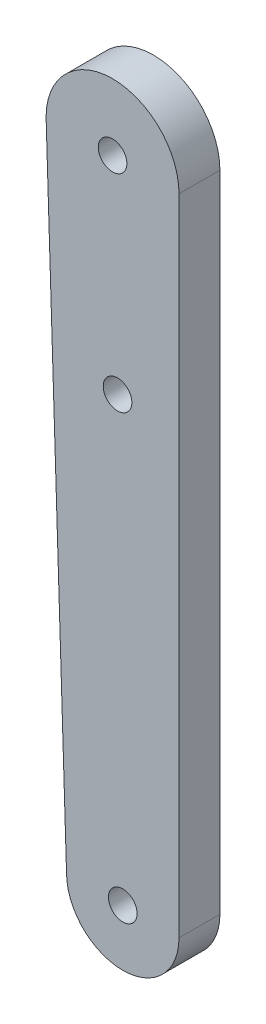
SolidWorks part; units mm, degrees
ref_plane "Front Plane" through (0, 0, 0) normal (0, 0, 1) x (1, 0, 0)
ref_plane "Top Plane" through (0, 0, 0) normal (0, 1, 0) x (1, 0, 0)
ref_plane "Right Plane" through (0, 0, 0) normal (1, 0, 0) x (0, 0, -1)
sketch "Sketch1" plane through (0, 0, 0) normal (0, 0, 1) x (1, 0, 0)
  line L6 (-0.0007, 1.9933) -> (-0.0007, 65.0161)
  line L7 (-13.0007, 65.0161) -> (-11.0007, 1.9933)
  arc A0 (-0.0007, 65.0161) -> (-13.0007, 65.0161) centre (-6.5007, 65.0161) ccw
  arc A1 (-11.0007, 1.9933) -> (-0.0007, 1.9933) centre (-5.5007, 1.9933) ccw
  circle A2 centre (-6.5007, 65.0161) radius 1.4
  circle A3 centre (-5.5007, 1.9933) radius 1.4
  circle A4 centre (-6.0128, 45.0161) radius 1.4
  point P8 (-5.0007, -3.4839)
  point P11 (-6.5007, 71.5161)
  dimension "D1" = 13
  dimension "D4" = 11
  dimension "D5" = 20
  dimension "D2" = 2.8
  dimension "D3" = 2.8
  dimension "D6" = 2.8
  dimension "D7" = 75
extrude "Boss-Extrude1" add sketch "Sketch1" along normal blind 4
